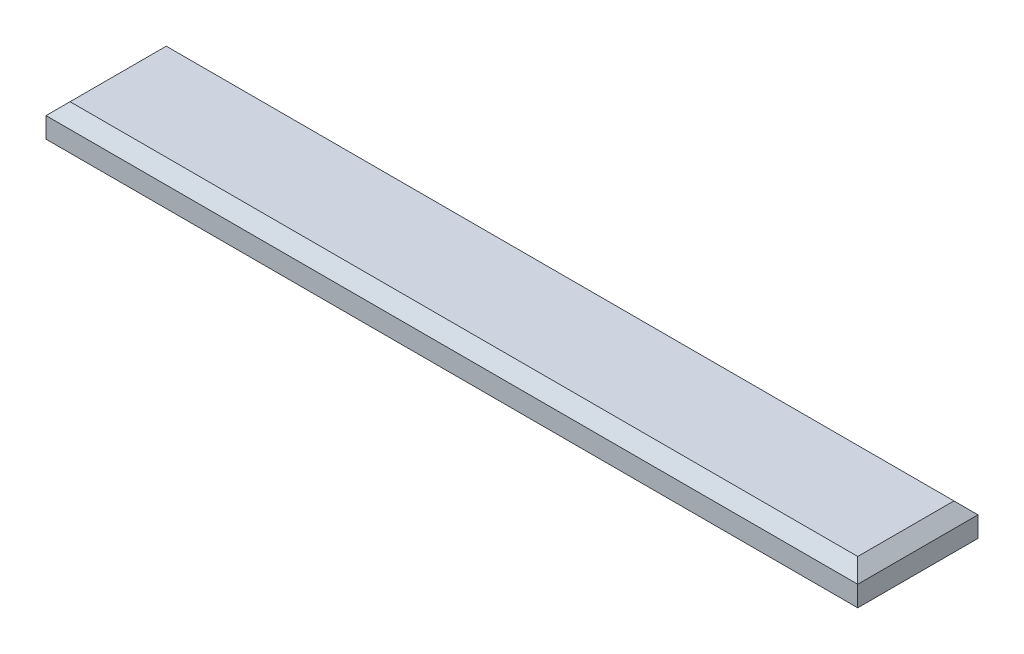
SolidWorks part; units mm, degrees
ref_plane "Front Plane" through (0, 0, 0) normal (0, 0, 1) x (1, 0, 0)
ref_plane "Top Plane" through (0, 0, 0) normal (0, 1, 0) x (1, 0, 0)
ref_plane "Right Plane" through (0, 0, 0) normal (1, 0, 0) x (0, 0, -1)
sketch "Sketch1" plane through (0, 0, 0) normal (0, 1, 0) x (1, 0, 0)
  line L1 (-67.5, -10) -> (67.5, -10)
  line L2 (-67.5, -10) -> (-67.5, 10)
  line L3 (-67.5, 10) -> (67.5, 10)
  line L4 (67.5, -10) -> (67.5, 10)
  line L5 (-67.5, -10) -> (67.5, 10) construction
  line L6 (-67.5, 10) -> (67.5, -10) construction
  point P0 (0, 0)
  dimension "D1" = 135
  dimension "D2" = 20
extrude "Boss-Extrude1" add sketch "Sketch1" along normal blind 5.4
chamfer "Chamfer1" distance 2 angle 45 4 edges at (0, 5.4, 10) (-67.5, 5.4, 0) (0, 5.4, -10) (67.5, 5.4, 0)
